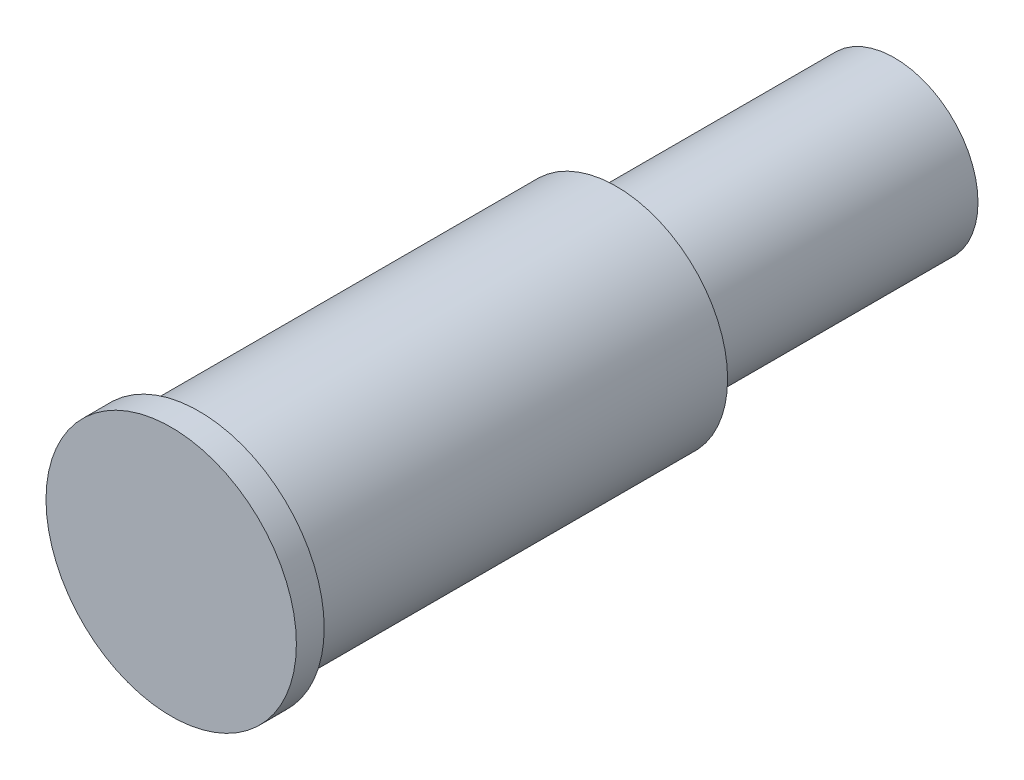
SolidWorks part; units mm, degrees
ref_plane "前视基准面" through (0, 0, 0) normal (0, 0, 1) x (1, 0, 0)
ref_plane "上视基准面" through (0, 0, 0) normal (0, 1, 0) x (1, 0, 0)
ref_plane "右视基准面" through (0, 0, 0) normal (1, 0, 0) x (0, 0, -1)
sketch "草图1" plane through (0, 0, 0) normal (0, 0, 1) x (1, 0, 0)
  circle A0 centre (0, 0) radius 3
  dimension "D1" = 6
extrude "凸台-拉伸1" add sketch "草图1" along normal blind 10
sketch "草图2" plane through (0, 0, 10) normal (0, 0, 1) x (1, 0, 0)
  circle A0 centre (0, 0) radius 4
  dimension "D1" = 8
extrude "凸台-拉伸2" add sketch "草图2" along normal blind 15
sketch "草图3" plane through (0, 0, 25) normal (0, 0, 1) x (1, 0, 0)
  circle A0 centre (0, 0) radius 4.5
  dimension "D1" = 9
extrude "凸台-拉伸3" add sketch "草图3" along normal blind 1
